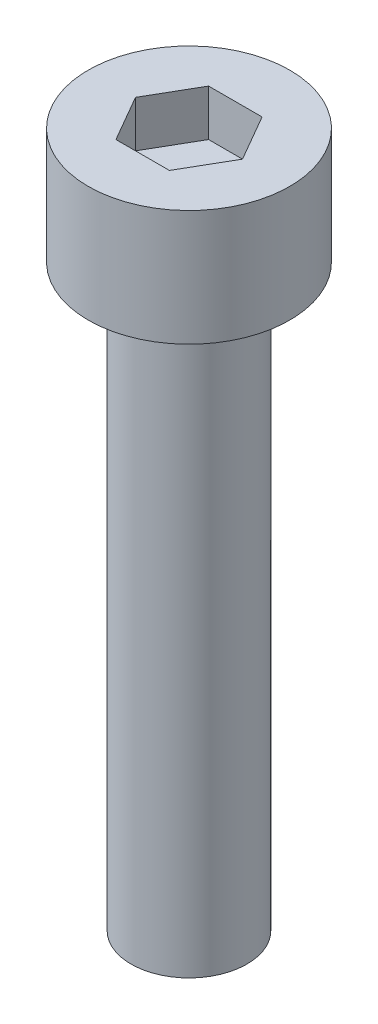
SolidWorks part; units mm, degrees
ref_plane "前视基准面" through (0, 0, 0) normal (0, 0, 1) x (1, 0, 0)
ref_plane "上视基准面" through (0, 0, 0) normal (0, 1, 0) x (1, 0, 0)
ref_plane "右视基准面" through (0, 0, 0) normal (1, 0, 0) x (0, 0, -1)
sketch "草图1" plane through (0, 0, 0) normal (0, 1, 0) x (1, 0, 0)
  circle A0 centre (0, 0) radius 4.35
  dimension "D1" = 8.7
extrude "凸台-拉伸1" add sketch "草图1" along normal blind 5
sketch "草图2" plane through (0, 5, 0) normal (0, 1, 0) x (1, 0, 0)
  line L1 (2.3094, 0) -> (1.1547, 2)
  line L2 (1.1547, 2) -> (-1.1547, 2)
  line L3 (-1.1547, 2) -> (-2.3094, 0)
  line L4 (-2.3094, 0) -> (-1.1547, -2)
  line L5 (-1.1547, -2) -> (1.1547, -2)
  line L6 (1.1547, -2) -> (2.3094, 0)
  circle A0 centre (0, 0) radius 2 construction
  dimension "D1" = 4
extrude "切除-拉伸1" cut sketch "草图2" against normal blind 2
sketch "草图3" plane through (0, 0, 0) normal (0, -1, 0) x (1, 0, 0)
  circle A0 centre (0, 0) radius 2.5
  dimension "D1" = 5
extrude "凸台-拉伸2" add sketch "草图3" along normal blind 25
